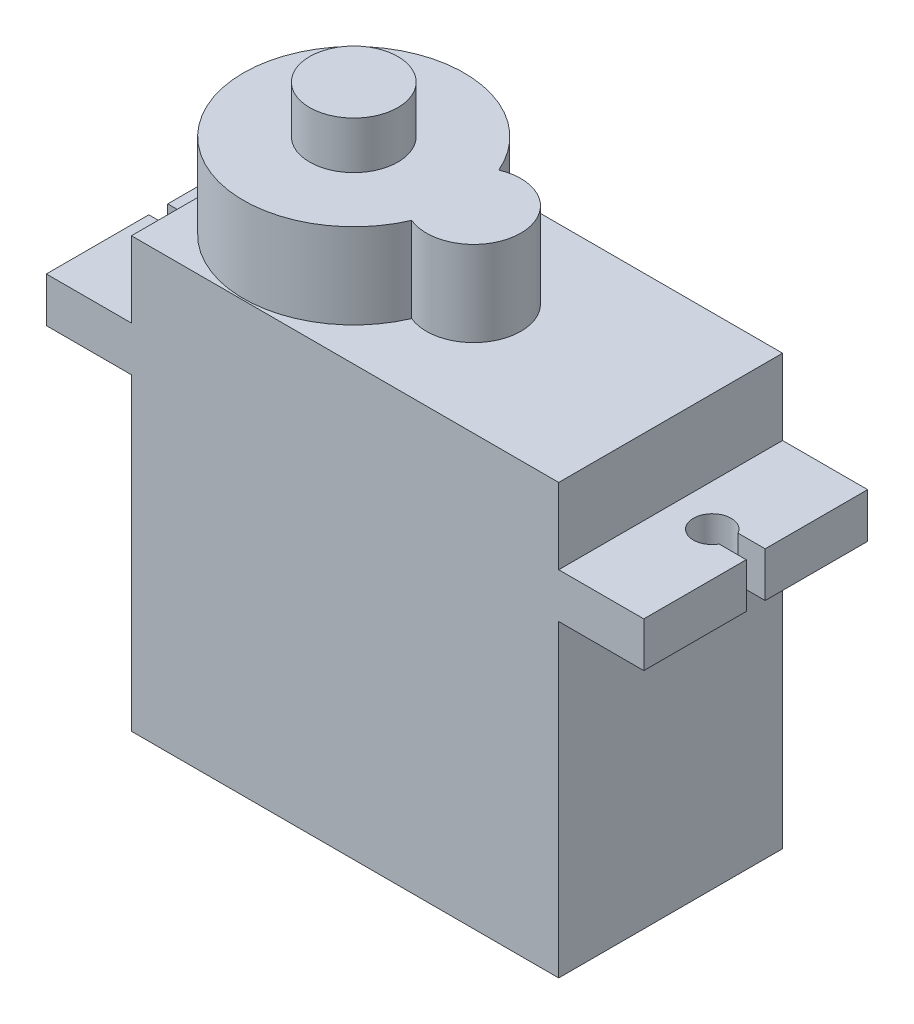
SolidWorks part; units mm, degrees
ref_plane "Front Plane" through (0, 0, 0) normal (0, 0, 1) x (1, 0, 0)
ref_plane "Top Plane" through (0, 0, 0) normal (0, 1, 0) x (1, 0, 0)
ref_plane "Right Plane" through (0, 0, 0) normal (1, 0, 0) x (0, 0, -1)
sketch "Sketch1" plane through (0, 0, 0) normal (0, 1, 0) x (1, 0, 0)
  line L1 (-46.1955, 4.5831) -> (-23.5955, 4.5831)
  line L2 (-46.1955, 4.5831) -> (-46.1955, -7.2569)
  line L3 (-46.1955, -7.2569) -> (-23.5955, -7.2569)
  line L4 (-23.5955, 4.5831) -> (-23.5955, -7.2569)
  dimension "D1" = 22.6
  dimension "D2" = 11.84
extrude "Boss-Extrude1" add sketch "Sketch1" along normal blind 22.7
ref_plane "Plane1" through (-23.5955, 22.7, -4.5831) normal (0, -1, 0) x (1, 0, 0)
sketch "Sketch2" plane through (-23.5955, 22.7, -4.5831) normal (0, -1, 0) x (1, 0, 0)
ref_plane "Plane2" through (-46.1955, 22.7, -4.5831) normal (0, 0, 1) x (1, 0, 0)
sketch "Sketch3" plane through (-46.1955, 22.7, -4.5831) normal (0, 0, 1) x (1, 0, 0)
sketch "Sketch4" plane through (0, 22.7, 0) normal (0, 1, 0) x (-1, 0, 0)
  line L0 (46.1955, 1.3369) -> (40.3555, 1.3369)
  line L1 (46.1955, -4.5831) -> (46.1955, 7.2569) construction
  circle A0 centre (40.3555, 1.3369) radius 5.84
extrude "Boss-Extrude6" add sketch "Sketch4" along normal blind 4.5
sketch "Sketch12" plane through (0, 27.2, 0) normal (0, 1, 0) x (-1, 0, 0)
  circle A0 centre (40.3555, 1.3369) radius 2.335
extrude "Boss-Extrude7" add sketch "Sketch12" along normal blind 2.5
sketch "Sketch13" plane through (0, 22.7, 0) normal (0, 1, 0) x (-1, 0, 0)
  line L0 (34.5155, 1.3369) -> (34.0155, 1.3369)
  circle A0 centre (40.3555, 1.3369) radius 5.84 construction
  circle A1 centre (34.0155, 1.3369) radius 2.5
extrude "Boss-Extrude8" add sketch "Sketch13" along normal blind 4.5
sketch "Sketch14" plane through (-23.5955, 0, 0) normal (1, 0, 0) x (0, 0, -1)
  line L0 (-7.2569, 22.7) -> (-7.2569, 18.7)
  line L1 (-7.2569, 22.7) -> (-7.2569, 0) construction
  line L2 (4.5831, 22.7) -> (4.5831, 0) construction
  line L3 (-7.2569, 18.7) -> (4.5831, 18.7)
  line L4 (-7.2569, 18.7) -> (-7.2569, 16.33)
  line L5 (-7.2569, 16.33) -> (4.5831, 16.33)
  line L6 (4.5831, 18.7) -> (4.5831, 16.33)
  line M2 (4.5831, 0) -> (4.5831, 22.7)
  line M4 (-7.2569, 22.7) -> (-7.2569, 0)
extrude "Boss-Extrude10" add sketch "Sketch14" along normal blind 4.5 contours L5 L3 M4 M2
sketch "Sketch15" plane through (0, 18.7, 0) normal (0, 1, 0) x (-1, 0, 0)
  line L0 (19.0955, 7.2569) -> (19.0955, -4.5831) construction
  line L1 (19.0955, 1.3369) -> (20.5955, 1.3369)
  line L2 (19.0955, 1.8369) -> (19.0955, 0.8369)
  line L3 (19.0955, 0.8369) -> (20.5955, 0.8369)
  line L4 (50.6955, 1.3369) -> (48.3955, 1.3369)
  line L5 (20.5955, 1.8369) -> (20.5955, 0.8369)
  line L6 (19.0955, 1.8369) -> (20.5955, 1.8369)
  line L7 (19.0955, 1.3369) -> (21.3955, 1.3369)
  circle A0 centre (21.3955, 1.3369) radius 1
  circle A1 centre (48.3955, 1.3369) radius 1
extrude "Cut-Extrude3" cut sketch "Sketch15" along direction (0, 1, 0) on the side against the normal through all
sketch "Sketch16" plane through (-46.1955, 0, 0) normal (-1, 0, 0) x (0, 0, 1)
  line L0 (7.2569, 22.7) -> (7.2569, 18.7)
  line L1 (7.2569, 22.7) -> (7.2569, 0) construction
  line L2 (7.2569, 18.7) -> (7.2569, 16.33)
  line L3 (7.2569, 18.7) -> (-4.5831, 18.7)
  line L4 (-4.5831, 22.7) -> (-4.5831, 0) construction
  line L5 (7.2569, 16.33) -> (-4.5831, 16.33)
  line M2 (7.2569, 0) -> (7.2569, 22.7)
  line M5 (-4.5831, 22.7) -> (-4.5831, 0)
extrude "Boss-Extrude11" add sketch "Sketch16" along normal blind 4.5 contours L5 L3 M2 M5
sketch "Sketch17" plane through (0, 18.7, 0) normal (0, 1, 0) x (-1, 0, 0)
  line L0 (50.6955, 0.8369) -> (50.6955, 1.8369)
  line L1 (50.6955, 1.3369) -> (49.1955, 1.3369)
  line L2 (50.6955, 1.8369) -> (49.1955, 1.8369)
  line L3 (49.1955, 0.8369) -> (49.1955, 1.8369)
  line L4 (50.6955, 7.2569) -> (50.6955, -4.5831) construction
  line L5 (50.6955, 0.8369) -> (49.1955, 0.8369)
  line L6 (50.6955, 1.3369) -> (48.2955, 1.3369)
  circle A0 centre (48.2955, 1.3369) radius 1
extrude "Cut-Extrude4" cut sketch "Sketch17" along direction (0, -1, 0) on the side against the normal through all
